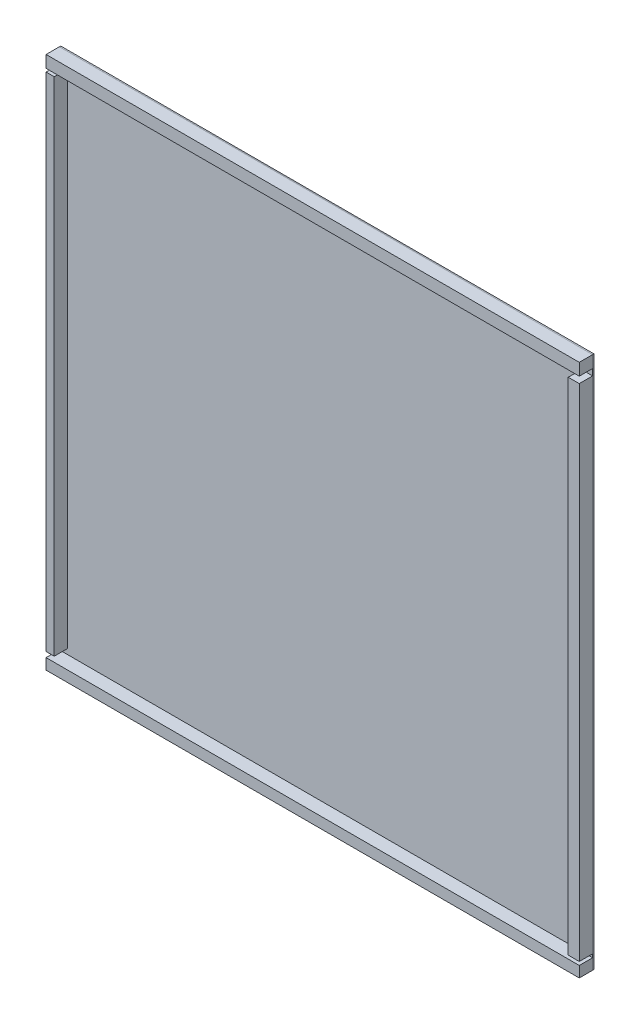
SolidWorks part; units mm, degrees
other "COLL.BOX-COLL.BOX-Boss-Extrude6"
other "COLL.BOX-COLL.BOX-Boss-Extrude5"
other "COLL.BOX-COLL.BOX-Boss-Extrude4"
other "COLL.BOX-COLL.BOX-Boss-Extrude3"
other "COLL.BOX-COLL.BOX-Boss-Extrude2"
ref_plane "Front Plane" through (0, 0, 0) normal (0, 0, 1) x (1, 0, 0)
ref_plane "Top Plane" through (0, 0, 0) normal (0, 1, 0) x (1, 0, 0)
ref_plane "Right Plane" through (0, 0, 0) normal (1, 0, 0) x (0, 0, -1)
sketch "Sketch1" plane through (0, 0, 0) normal (0, 0, 1) x (1, 0, 0)
  line L1 (-250, 3750) -> (3750, 3750)
  line L2 (-250, 3750) -> (-250, -250)
  line L3 (-250, -250) -> (3750, -250)
  line L4 (3750, 3750) -> (3750, -250)
  dimension "D1" = 4000
  dimension "D2" = 4000
  dimension "D3" = 250
  dimension "D4" = 250
extrude "Boss-Extrude1" add sketch "Sketch1" along normal blind 10
sketch "Sketch2" plane through (0, 0, 10) normal (0, 0, 1) x (1, 0, 0)
  line L1 (-250, 3750) -> (3750, 3750)
  line L2 (-250, 3750) -> (-250, -250)
  line L3 (-250, -250) -> (3750, -250)
  line L4 (3750, 3750) -> (3750, -250)
extrude "Boss-Extrude2" add sketch "Sketch2" against normal up to next (10 mm away) separate body
sketch "Sketch3" plane through (0, 0, 10) normal (0, 0, 1) x (1, 0, 0)
  line L0 (3750, -250) -> (3750, 3750) construction
  line L1 (-250, 3750) -> (3750, 3750)
  line L2 (-250, 3750) -> (-250, 3659.8759)
  line L3 (-250, 3659.8759) -> (3750, 3659.8759)
  line L4 (3750, 3750) -> (3750, 3659.8759)
extrude "Boss-Extrude3" add sketch "Sketch3" along normal blind 100 separate body
sketch "Sketch4" plane through (0, 0, 10) normal (0, 0, 1) x (1, 0, 0)
  line L0 (-250, 3750) -> (-250, -250) construction
  line L1 (3750, -250) -> (-250, -250)
  line L2 (3750, -250) -> (3750, -168.4149)
  line L3 (3750, -168.4149) -> (-250, -168.4149)
  line L4 (-250, -250) -> (-250, -168.4149)
extrude "Boss-Extrude4" add sketch "Sketch4" along normal blind 100 separate body
sketch "Sketch5" plane through (0, 0, 10) normal (0, 0, 1) x (1, 0, 0)
  line L0 (3750, -250) -> (3750, 3750) construction
  line L1 (3750, 3611.6589) -> (3667.2953, 3611.6589)
  line L2 (3750, 3611.6589) -> (3750, -142.8735)
  line L3 (3750, -142.8735) -> (3667.2953, -142.8735)
  line L4 (3667.2953, 3611.6589) -> (3667.2953, -142.8735)
extrude "Boss-Extrude5" add sketch "Sketch5" along normal blind 100 separate body
sketch "Sketch6" plane through (0, 0, 10) normal (0, 0, 1) x (1, 0, 0)
  line L0 (-250, 3750) -> (-250, -250) construction
  line L1 (-250, 3635.8382) -> (-188.9916, 3635.8382)
  line L2 (-250, 3635.8382) -> (-250, -128.9914)
  line L3 (-250, -128.9914) -> (-188.9916, -128.9914)
  line L4 (-188.9916, 3635.8382) -> (-188.9916, -128.9914)
extrude "Boss-Extrude6" add sketch "Sketch6" along normal blind 100 separate body
sketch "Sketch8" plane through (0, 0, 10) normal (0, 0, 1) x (1, 0, 0)
  line L3 (3750, 3750) -> (1750, 3750)
  line L5 (3750, 3750) -> (3750, 1750)
  line L6 (3750, 1750) -> (1750, 1750)
  line L7 (1750, 3750) -> (1750, 1750)
  dimension "D1" = 2000
  dimension "D2" = 2000
